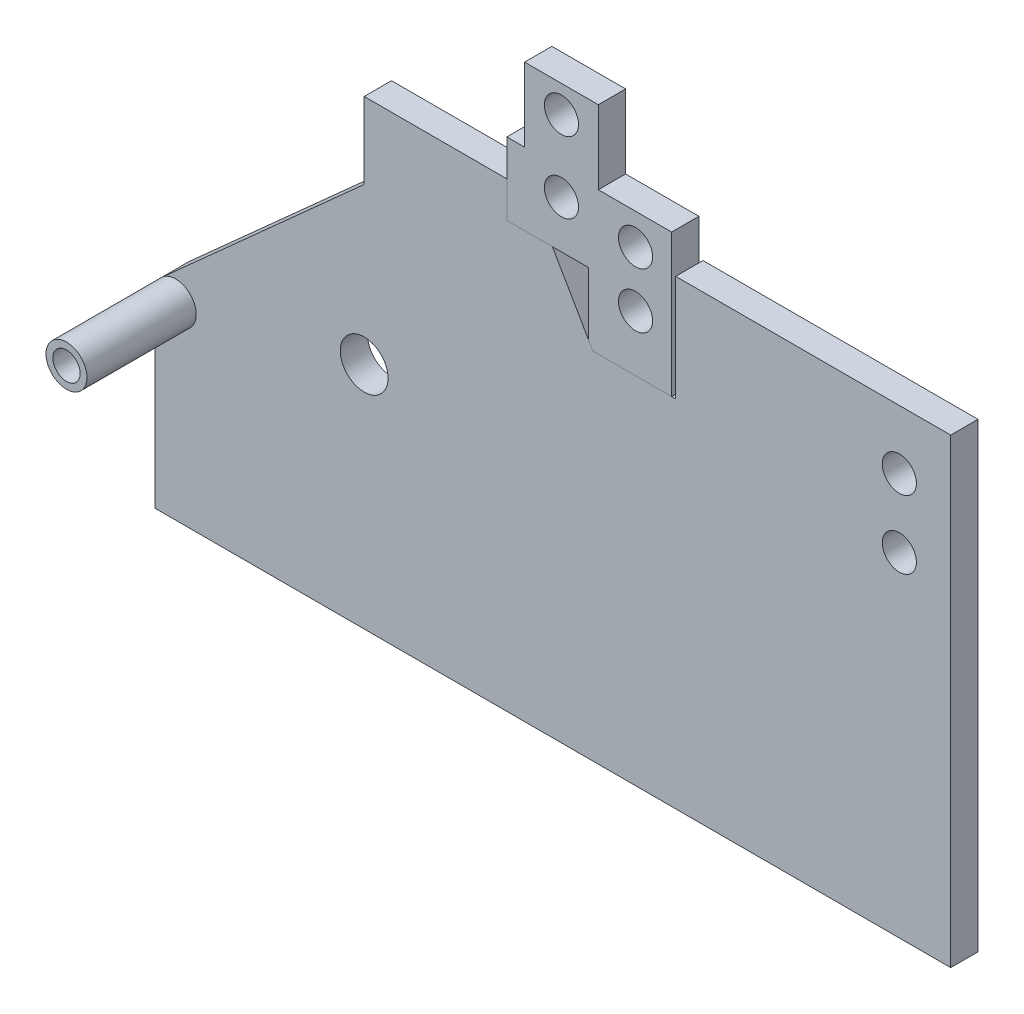
SolidWorks part; units mm, degrees
ref_plane "Front Plane" through (0, 0, 0) normal (0, 0, 1) x (1, 0, 0)
ref_plane "Top Plane" through (0, 0, 0) normal (0, 1, 0) x (1, 0, 0)
ref_plane "Right Plane" through (0, 0, 0) normal (1, 0, 0) x (0, 0, -1)
sketch "Sketch1" plane through (0, 0, 0) normal (0, 0, 1) x (1, 0, 0)
  line L0 (-54.9958, 0) -> (67.63, 0) construction
  line L1 (0, 23.262) -> (0, -27.492) construction
  line L2 (0, 0) -> (582.5, 0)
  line L3 (0, 0) -> (0, 138)
  line L4 (582.5, 0) -> (582.5, 51.1837)
  line L5 (522.5, 60) -> (572.5, 51.1837)
  line L6 (582.5, 51.1837) -> (572.5, 51.1837)
  line L8 (4.9848, 149.1667) -> (129.7305, 261.0488)
  line L10 (129.7305, 261.0488) -> (153, 281.9188)
  line L11 (153, 281.9188) -> (153, 337.7402)
  line L13 (244.94, 310.7333) -> (374.6494, 86.07)
  line L15 (522.5, 60) -> (374.6494, 86.07)
  circle A0 centre (15, 138) radius 15
  circle A2 centre (15, 138) radius 10
  arc A4 (244.94, 310.7333) -> (153, 337.7402) centre (153, 167.7402) ccw
  circle A5 centre (153, 167.7402) radius 17.5
  point P15 (153, 167.7402)
  dimension "D3" = 30
  dimension "D2" = 170
extrude "Boss-Extrude1" add sketch "Sketch1" along normal blind 20
sketch "Sketch2" plane through (0, 0, 20) normal (0, 0, 1) x (1, 0, 0)
  circle A0 centre (15, 138) radius 10
  circle A1 centre (15, 138) radius 15
extrude "Boss-Extrude2" add sketch "Sketch2" along normal blind 80
sketch "Sketch3" plane through (0, 0, 0) normal (0, 0, -1) x (-1, 0, 0)
  circle A0 centre (-15, 138) radius 24.4466
  circle A1 centre (-153, 167.7402) radius 60.5372
sketch "Sketch4" plane through (0, 0, 20) normal (0, 0, 1) x (1, 0, 0)
  line L0 (153, 167.7402) -> (535.4044, 167.7402) construction
  line L1 (153, 167.7402) -> (153, 389.688) construction
  line L2 (153, 167.7402) -> (281.8848, 326.8997) construction
  line L3 (426.1731, 76.985) -> (522.5, 60)
  line L8 (153, 337.7402) -> (257.4605, 337.7402)
  line L9 (0, 0) -> (582.5, 0) construction
  line L10 (290.8428, 311.384) -> (426.1731, 76.985)
  line L11 (244.94, 310.7333) -> (374.6494, 86.07) construction
  line L12 (374.6494, 86.07) -> (426.1731, 76.985)
  line L13 (374.6494, 86.07) -> (244.94, 310.7333)
  line L18 (290.8428, 311.384) -> (257.4605, 311.384)
  line L19 (257.4605, 337.7402) -> (257.4605, 311.384)
  arc A4 (244.94, 310.7333) -> (153, 337.7402) centre (153, 167.7402) ccw
  line M13 (572.5, 51.1837) -> (374.6494, 86.07)
  line M14 (374.6494, 86.07) -> (244.94, 310.7333)
  arc M15 (244.94, 310.7333) -> (153, 337.7402) centre (153, 167.7402) ccw
  dimension "D1" = 51
extrude "Boss-Extrude6" add sketch "Sketch4" against normal blind 20 contours L19 L8 L10 L18 M15 M14 M13
sketch "Sketch9" plane through (0, 0, 20) normal (0, 0, 1) x (1, 0, 0)
  line L2 (290.8428, 311.384) -> (426.1731, 76.985) construction
  line L3 (582.5, 337.7402) -> (582.5, 51.1837)
  line L4 (320.5094, 260) -> (426.1731, 76.985)
  line L5 (426.1731, 76.985) -> (522.5, 60)
  line L6 (320.5094, 260) -> (381.1194, 260)
  line L7 (381.1194, 260) -> (381.1194, 337.7402)
  line L8 (381.1194, 337.7402) -> (525.48, 337.7402)
  line L11 (582.5, 337.7402) -> (525.48, 337.7402)
  line L12 (522.5, 60) -> (572.5, 51.1837)
  line L13 (582.5, 51.1837) -> (572.5, 51.1837)
  dimension "D1" = 60.61
extrude "Boss-Extrude7" add sketch "Sketch9" against normal blind 20
sketch "Sketch10" plane through (0, 0, 20) normal (0, 0, 1) x (1, 0, 0)
  line L0 (257.4605, 364.3202) -> (257.4605, 337.7402)
  line L1 (257.4605, 364.3202) -> (317.1805, 364.3202)
  line L2 (317.1805, 364.3202) -> (317.1805, 311.384)
  line L3 (257.4605, 311.384) -> (317.1805, 311.384)
  line L4 (257.4605, 337.7402) -> (257.4605, 311.384)
  line L5 (324.4605, 418.2516) -> (324.4605, 364.3202)
  line L9 (347.6505, 321.2239) -> (317.1805, 321.2239)
  line L10 (347.6505, 321.2239) -> (378.1205, 321.2239)
  line L11 (378.1205, 321.2239) -> (378.1205, 364.3202)
  line L12 (378.1205, 364.3202) -> (317.1805, 364.3202)
  line L13 (270.4605, 364.3202) -> (270.4605, 418.2516)
  line L14 (270.4605, 418.2516) -> (324.4605, 418.2516)
  line L16 (378.1205, 321.2239) -> (378.1205, 260)
  line L17 (378.1205, 260) -> (320.5094, 260)
  line L18 (317.1805, 265.7096) -> (317.1805, 311.384)
  line L19 (320.5094, 260) -> (317.1805, 265.7096)
  line L21 (290.8428, 311.384) -> (257.4605, 311.384) construction
  circle A0 centre (297.4605, 346.134) radius 12.5
  circle A1 centre (351.7105, 341.56) radius 12.5
  circle A2 centre (351.7105, 301) radius 12.5
  circle A3 centre (297.4605, 398.384) radius 12.5
  dimension "D2" = 54.25
  dimension "D1" = 40.56
extrude "Boss-Extrude9" add sketch "Sketch10" against normal blind 20 separate body
sketch "Sketch11" plane through (0, 0, 0) normal (0, 0, -1) x (-1, 0, 0)
  line L0 (-351.7105, 301) -> (-351.7105, 341.56) construction
  line L1 (-351.7105, 321.28) -> (-424.2848, 321.28) construction
  line L2 (-351.7105, 321.28) -> (-544.8957, 269.5162) construction
  line L3 (-544.8957, 269.5162) -> (-544.8957, 294.5162) construction
  line L4 (-544.8957, 269.5162) -> (-544.8957, 244.5162) construction
  circle A0 centre (-544.8957, 294.5162) radius 12.5
  circle A1 centre (-544.8957, 244.5162) radius 12.5
  dimension "D1" = 15
  dimension "D2" = 200
  dimension "D3" = 25
  dimension "D4" = 25
extrude "Cut-Extrude1" cut sketch "Sketch11" against normal blind 20
